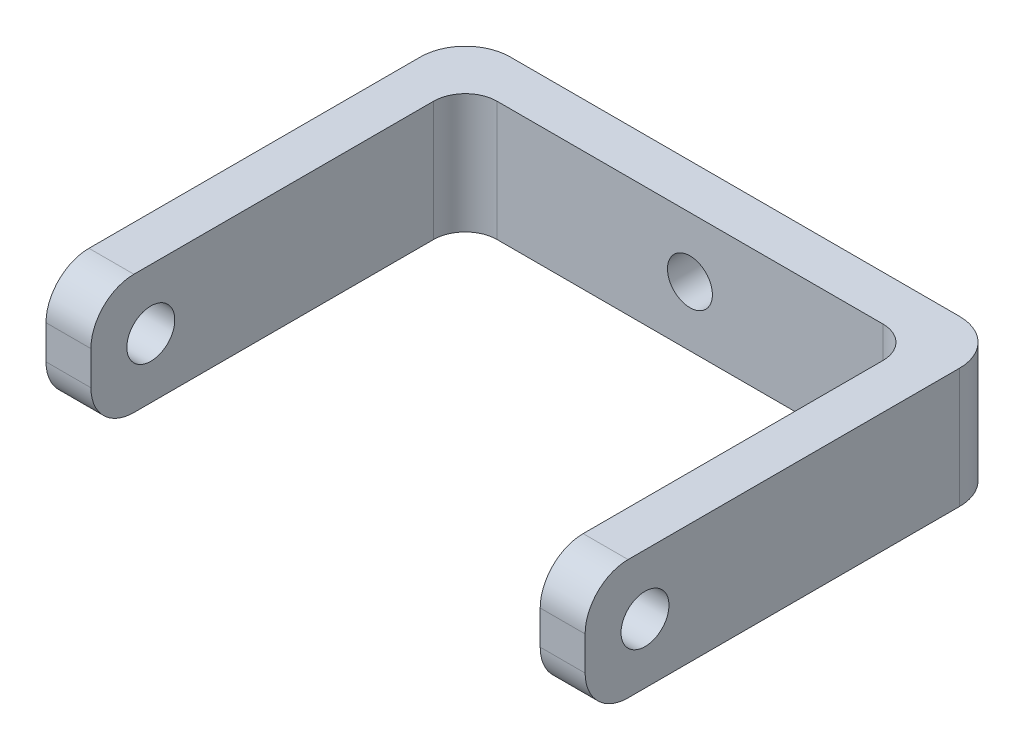
SolidWorks part; units mm, degrees
ref_plane "Front Plane" through (0, 0, 0) normal (0, 0, 1) x (1, 0, 0)
ref_plane "Top Plane" through (0, 0, 0) normal (0, 1, 0) x (1, 0, 0)
ref_plane "Right Plane" through (0, 0, 0) normal (1, 0, 0) x (0, 0, -1)
sketch "Sketch1" plane through (0, 0, 0) normal (0, 1, 0) x (1, 0, 0)
  line L0 (0, 0) -> (-3, 0)
  line L1 (0, 0) -> (30, 0)
  line L2 (0, 0) -> (0, 25)
  line L3 (0, 25) -> (30, 25)
  line L4 (30, 0) -> (30, 25)
  line L5 (-3, 0) -> (-3, 28)
  line L6 (-3, 28) -> (33, 28)
  line L7 (33, 28) -> (33, 0)
  line L8 (33, 0) -> (30, 0)
  line L9 (-3, 28) -> (0, 25)
  line L10 (0, 25) -> (2.1213, 22.8787)
  line L11 (33, 28) -> (30, 25)
  line L12 (30, 25) -> (27.8787, 22.8787)
  circle A0 centre (2.1213, 22.8787) radius 2.1213
  circle A1 centre (27.8787, 22.8787) radius 2.1213
  circle A2 centre (0, 25) radius 3
  circle A3 centre (30, 25) radius 3
extrude "Boss-Extrude1" add sketch "Sketch1" along normal blind 8 contours A2 L5 L0 L2 | L9 A2 L2 | L3 A2 L9 | A3 L6 A2 L3 | A0 L3 L10 | A0 L10 L2 | L11 A3 L3 | A1 L12 L3 | A1 L4 L12 | L4 A3 L11 | A3 L4 L8 L7
sketch "Sketch2" plane through (-3, 0, 0) normal (-1, 0, 0) x (0, 0, 1)
  line L0 (0, 0) -> (-8, 8)
  line L1 (0, 8) -> (-25, 8) construction
  circle A0 centre (-4, 4) radius 1.6
extrude "Cut-Extrude1" cut sketch "Sketch2" against normal through all both and the other way through all contours L0 A0 | L0 A0
sketch "Sketch3" plane through (-3, 0, 0) normal (-1, 0, 0) x (0, 0, 1)
  line L0 (-4, 4) -> (-2.8686, 2.8686)
  line L1 (-2.8686, 2.8686) -> (-2.8686, 5.1314)
  line L2 (-2.8686, -5.3532) -> (-2.8686, 14.5194)
  circle A0 centre (-4, 4) radius 1.6 construction
  circle A1 centre (-2.8686, 2.8686) radius 2.8686
  circle A2 centre (-2.8686, 5.1314) radius 2.8686
  circle A3 centre (-2.8686, 4) radius 7.2347
  line M2 (-25, 0) -> (0, 0)
  line M3 (0, 0) -> (0, 8)
  line M4 (0, 8) -> (-25, 8)
extrude "Cut-Extrude2" cut sketch "Sketch3" against normal through all both and the other way through all contours L2 A3 M4 M3 M2 | A1 M2 M3 | A2 M3 M4
sketch "Sketch4" plane through (0, 0, -28) normal (0, 0, -1) x (-1, 0, 0)
  line L0 (0, 8) -> (-30, 0)
  circle A0 centre (-15, 4) radius 1.5
extrude "Cut-Extrude6" cut sketch "Sketch4" against normal blind 5 contours L0 A0 | L0 A0
